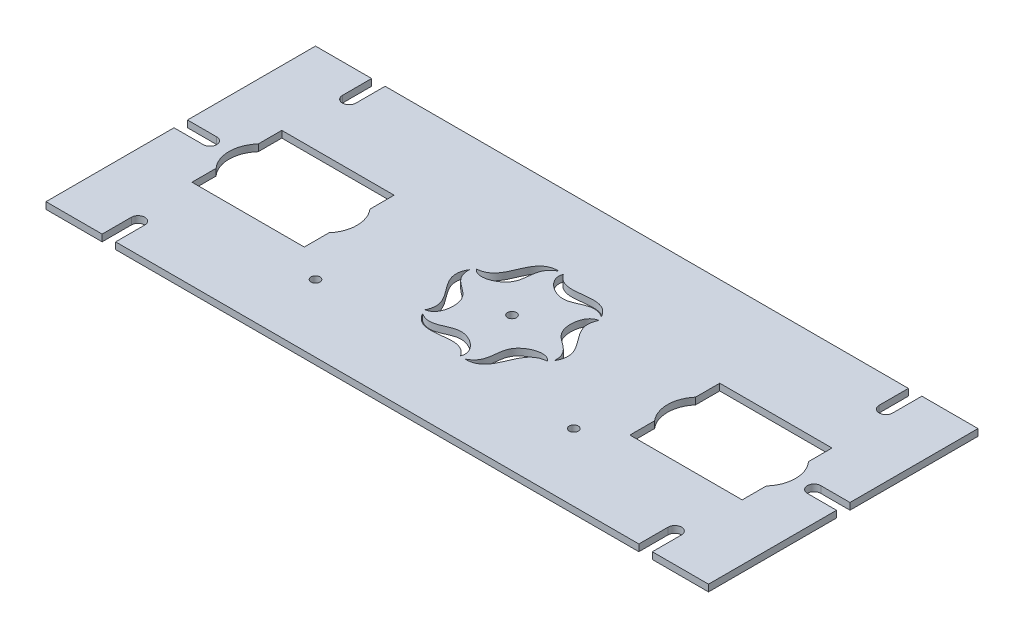
SolidWorks part; units mm, degrees
ref_plane "Front Plane" through (0, 0, 0) normal (0, 0, 1) x (1, 0, 0)
ref_plane "Top Plane" through (0, 0, 0) normal (0, 1, 0) x (1, 0, 0)
ref_plane "Right Plane" through (0, 0, 0) normal (1, 0, 0) x (0, 0, -1)
sketch "Sketch1" plane through (0, 0, 0) normal (0, 1, 0) x (1, 0, 0)
  line L1 (-147.5, -60) -> (147.5, -60)
  line L2 (-147.5, -60) -> (-147.5, 60)
  line L3 (-147.5, 60) -> (147.5, 60)
  line L4 (147.5, -60) -> (147.5, 60)
  line L5 (-147.5, -60) -> (147.5, 60) construction
  line L6 (-147.5, 60) -> (147.5, -60) construction
  point P0 (0, 0)
  dimension "D1" = 295
  dimension "D2" = 120
extrude "Boss-Extrude1" add sketch "Sketch1" along normal blind 3
sketch "Sketch2" plane through (0, 3, 0) normal (0, 1, 0) x (1, 0, 0)
  line L0 (0, -60) -> (0, 60) construction
  line L1 (147.5, 60) -> (-147.5, 60) construction
  line L2 (0, 60) -> (0, -60) construction
  line L3 (-147.5, 0) -> (147.5, 0) construction
  line L4 (147.5, -60) -> (147.5, 60) construction
  line L5 (-122.5, 60) -> (-122.5, 47)
  line L6 (-116.5, 47) -> (-116.5, 60)
  line L7 (-116.5, 60) -> (-122.5, 60)
  line L8 (-147.5, 60) -> (-147.5, -60) construction
  line L9 (116.5, 60) -> (122.5, 60)
  line L10 (116.5, 47) -> (116.5, 60)
  line L11 (122.5, 60) -> (122.5, 47)
  line L12 (122.5, -60) -> (122.5, -47)
  line L13 (116.5, -47) -> (116.5, -60)
  line L14 (116.5, -60) -> (122.5, -60)
  line L15 (-116.5, -60) -> (-122.5, -60)
  line L16 (-116.5, -47) -> (-116.5, -60)
  line L17 (-122.5, -60) -> (-122.5, -47)
  line L18 (147.5, 3) -> (134.5, 3)
  line L19 (134.5, -3) -> (147.5, -3)
  line L20 (147.5, -3) -> (147.5, 3)
  line L21 (-147.5, -3) -> (-147.5, 3)
  line L22 (-134.5, -3) -> (-147.5, -3)
  line L23 (-147.5, 3) -> (-134.5, 3)
  arc A0 (-122.5, 47) -> (-116.5, 47) centre (-119.5, 47) ccw
  arc A1 (122.5, 47) -> (116.5, 47) centre (119.5, 47) cw
  arc A2 (122.5, -47) -> (116.5, -47) centre (119.5, -47) ccw
  arc A3 (-122.5, -47) -> (-116.5, -47) centre (-119.5, -47) cw
  arc A4 (134.5, 3) -> (134.5, -3) centre (134.5, 0) ccw
  arc A5 (-134.5, 3) -> (-134.5, -3) centre (-134.5, 0) cw
  point P43 (0, 0)
  dimension "D5" = 3
  dimension "D1" = 6
  dimension "D2" = 13
  dimension "D3" = 25
  dimension "D4" = 13
extrude "Cut-Extrude1" cut sketch "Sketch2" against normal blind 10
sketch "Sketch3" plane through (0, 3, 0) normal (0, 1, 0) x (1, 0, 0)
  circle A3 centre (0, 0) radius 36 construction
  circle A4 centre (0, 0) radius 2
  spline S0 degree 3 poles (-6.4103, 27.4171) (-18.6703, 27.6041) (-14.2586, 10.5602) (-25.6947, 9.9025) knots 0 0 0 0 1 1 1 1
  spline S1 degree 3 poles (-25.6947, 9.9025) (-22.7475, 6.0724) (-7.1755, 11.9426) (-13.1998, 24.0317) (-6.4103, 27.4171) knots 0 0 0 0 0.463038 1 1 1 1
  spline S2 degree 3 poles (-4.2715, 27.2035) (-6.1149, 22.7361) (6.7548, 12.1855) (14.2121, 23.4472) (20.5388, 19.2601) knots 0 0 0 0 0.463038 1 1 1 1
  spline S3 degree 3 poles (20.5388, 19.2601) (14.5707, 29.971) (2.0161, 17.6285) (-4.2715, 27.2035) knots 0 0 0 0 1 1 1 1
  spline S4 degree 3 poles (21.4232, 17.301) (16.6326, 16.6637) (13.9303, 0.2429) (27.412, -0.5845) (26.9491, -8.157) knots 0 0 0 0 0.463038 1 1 1 1
  spline S5 degree 3 poles (26.9491, -8.157) (33.241, 2.3669) (16.2747, 7.0682) (21.4232, 17.301) knots 0 0 0 0 1 1 1 1
  spline S6 degree 3 poles (25.6947, -9.9025) (22.7475, -6.0724) (7.1755, -11.9426) (13.1998, -24.0317) (6.4103, -27.4171) knots 0 0 0 0 0.463038 1 1 1 1
  spline S7 degree 3 poles (6.4103, -27.4171) (18.6703, -27.6041) (14.2586, -10.5602) (25.6947, -9.9025) knots 0 0 0 0 1 1 1 1
  spline S8 degree 3 poles (4.2715, -27.2035) (6.1149, -22.7361) (-6.7548, -12.1855) (-14.2121, -23.4472) (-20.5388, -19.2601) knots 0 0 0 0 0.463038 1 1 1 1
  spline S9 degree 3 poles (-20.5388, -19.2601) (-14.5707, -29.971) (-2.0161, -17.6285) (4.2715, -27.2035) knots 0 0 0 0 1 1 1 1
  spline S10 degree 3 poles (-21.4232, -17.301) (-16.6326, -16.6637) (-13.9303, -0.2429) (-27.412, 0.5845) (-26.9491, 8.157) knots 0 0 0 0 0.463038 1 1 1 1
  spline S11 degree 3 poles (-26.9491, 8.157) (-33.241, -2.3669) (-16.2747, -7.0682) (-21.4232, -17.301) knots 0 0 0 0 1 1 1 1
  point P48 (0, 0)
  dimension "D1" = 72
  dimension "D2" = 4
extrude "Cut-Extrude3" cut sketch "Sketch3" against normal blind 10
sketch "Sketch4" plane through (0, 3, 0) normal (0, 1, 0) x (1, 0, 0)
  line L0 (-147.5, 60) -> (-147.5, 3) construction
  line L1 (-122.5, 20) -> (-72.5, 20)
  line L2 (-122.5, 20) -> (-122.5, -20)
  line L3 (-122.5, -20) -> (-72.5, -20)
  line L4 (-72.5, 20) -> (-72.5, -20)
  line L5 (-122.5, 20) -> (-72.5, -20) construction
  line L6 (-122.5, -20) -> (-72.5, 20) construction
  line L7 (-116.5, -60) -> (116.5, -60) construction
  line L8 (0, 60) -> (0, -60) construction
  line L9 (116.5, 60) -> (-116.5, 60) construction
  line L10 (122.5, 20) -> (122.5, -20)
  line L11 (122.5, -20) -> (72.5, -20)
  line L12 (72.5, 20) -> (72.5, -20)
  line L13 (122.5, 20) -> (72.5, 20)
  point P0 (-97.5, 0)
  dimension "D1" = 50
  dimension "D2" = 40
  dimension "D3" = 50
  dimension "D4" = 40
extrude "Cut-Extrude4" cut sketch "Sketch4" against normal blind 10
sketch "Sketch5" plane through (0, 0, 0) normal (0, -1, 0) x (1, 0, 0)
  circle A0 centre (-112.125, -0.125) radius 11 construction
  circle A1 centre (-83.125, -0.125) radius 11 construction
  circle A2 centre (-112.125, -0.125) radius 11
  circle A3 centre (-83.125, -0.125) radius 11
  circle A4 centre (-83.125, -0.125) radius 14
  circle A5 centre (-112.125, -0.125) radius 14
  line M1 (-72.5, 20) -> (-72.5, -20)
  line M3 (-122.5, -20) -> (-122.5, 20)
  dimension "D1" = 3
sketch "Sketch6" plane through (0, 3, 0) normal (0, 1, 0) x (1, 0, 0)
  circle A0 centre (0, 0) radius 36
  dimension "D1" = 72
extrude "Cut-Extrude5" cut sketch "Sketch5" against normal blind 10 contours A3 M1 | A2 M3 | A5 A2 M3 | A4 A3 M1 | A5 A2 M3 | A2 M3 | A4 A3 M1 | A3 M1
mirror "Mirror1" about plane through (0, 0, 0) normal (1, 0, 0) of "Cut-Extrude5"
sketch "Sketch7" plane through (0, 0, 0) normal (0, -1, 0) x (1, 0, 0)
  line L0 (0, 0) -> (0, 60) construction
  line L1 (-116.5, 60) -> (116.5, 60) construction
  line L2 (147.5, 60) -> (147.5, 3) construction
  circle A0 centre (57.5, 30) radius 2
  circle A1 centre (-57.5, 30) radius 2
  dimension "D1" = 4
  dimension "D2" = 30
  dimension "D3" = 90
extrude "Cut-Extrude6" cut sketch "Sketch7" against normal blind 10
